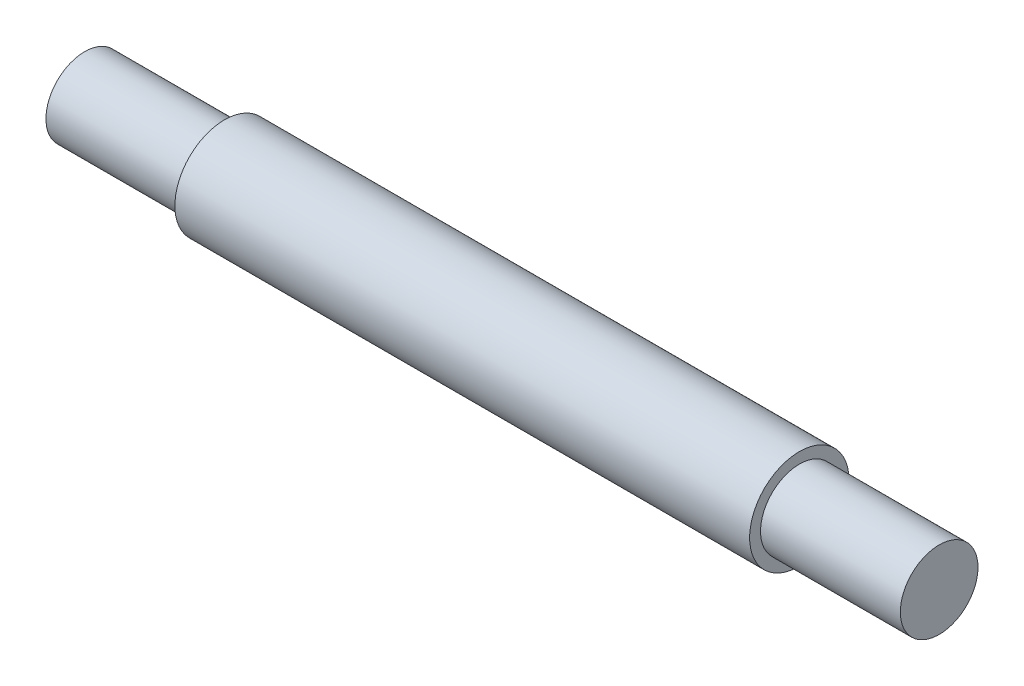
SolidWorks part; units mm, degrees
material "Brass"
ref_plane "Front Plane" through (0, 0, 0) normal (0, 0, 1) x (1, 0, 0)
ref_plane "Top Plane" through (0, 0, 0) normal (0, 1, 0) x (1, 0, 0)
ref_plane "Right Plane" through (0, 0, 0) normal (1, 0, 0) x (0, 0, -1)
sketch "Sketch1" plane through (0, 0, 0) normal (1, 0, 0) x (0, 0, -1)
  circle A0 centre (0, 0) radius 3.175
  dimension "D1" = 6.35
extrude "Boss-Extrude1" add sketch "Sketch1" along normal mid plane 69.85
sketch "Sketch2" plane through (0, 0, 0) normal (1, 0, 0) x (0, 0, -1)
  circle A0 centre (0, 0) radius 4.064
  dimension "D1" = 8.128
extrude "Boss-Extrude2" add sketch "Sketch2" along normal mid plane 46.99
